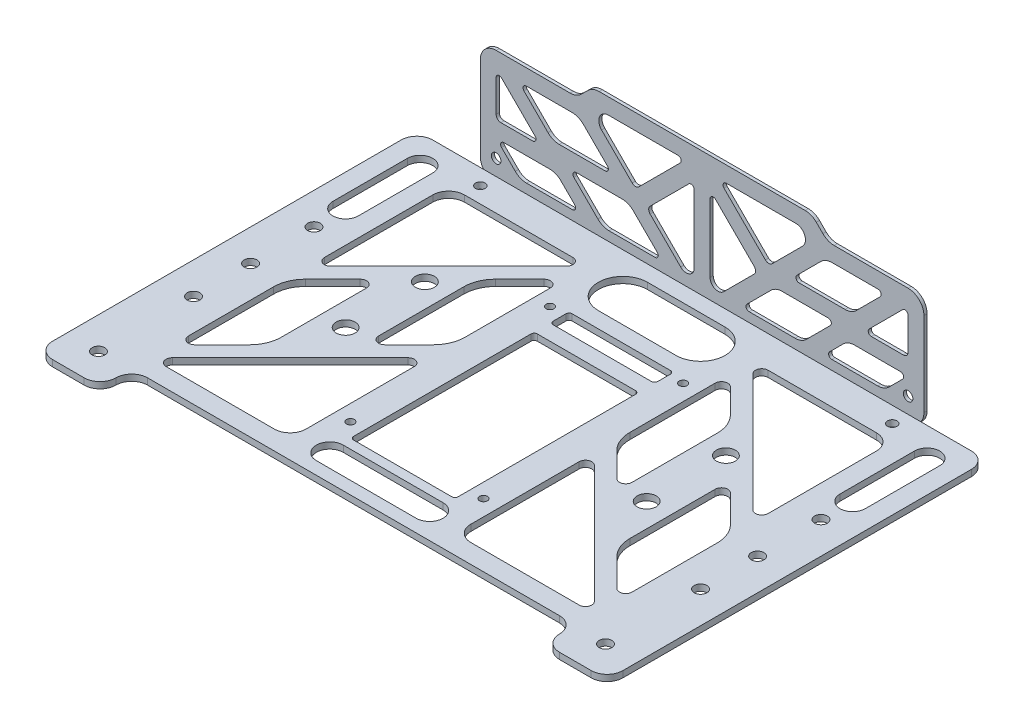
SolidWorks part; units mm, degrees
material "Thornel Mat VMA"
ref_plane "前视基准面" through (0, 0, 0) normal (0, 0, 1) x (1, 0, 0)
ref_plane "上视基准面" through (0, 0, 0) normal (0, 1, 0) x (1, 0, 0)
ref_plane "右视基准面" through (0, 0, 0) normal (1, 0, 0) x (0, 0, -1)
sketch "草图1" plane through (0, 0, 0) normal (0, 1, 0) x (1, 0, 0)
  line L19 (-21, 31.5) -> (21, 31.5) construction
  line L20 (-21, 31.5) -> (-21, -31.5) construction
  line L21 (-21, -31.5) -> (21, -31.5) construction
  line L22 (21, 31.5) -> (21, -31.5) construction
  line L24 (-85, 58.5) -> (85, 58.5)
  line L25 (-90, 53.5) -> (-90, -56.5)
  line L26 (-85, -61.5) -> (-75, -61.5)
  line L28 (0, 0) -> (0, 58.5) construction
  line L29 (-21, 0) -> (0, 0) construction
  line L31 (-65, -51.5) -> (65, -51.5)
  line L33 (-80, -61.5) -> (-80, 58.5) construction
  line L34 (0, -55) -> (0, 55) construction
  line L36 (85, -61.5) -> (75, -61.5)
  line L37 (90, 53.5) -> (90, -56.5)
  line L38 (-70, -56.5) -> (-70, -32.8054) construction
  line L40 (-47.5, 18.5) -> (47.5, 18.5) construction
  line L41 (-47.5, 18.5) -> (-47.5, -6.5) construction
  line L42 (-47.5, -6.5) -> (47.5, -6.5) construction
  line L43 (47.5, 18.5) -> (47.5, -6.5) construction
  circle A6 centre (-21, 31.5) radius 1.25
  circle A7 centre (-21, -31.5) radius 1.25
  circle A8 centre (21, -31.5) radius 1.25
  circle A9 centre (21, 31.5) radius 1.25
  circle A10 centre (-80, -52) radius 2
  circle A11 centre (80, -52) radius 2
  arc A12 (-75, -61.5) -> (-70, -56.5) centre (-75, -56.5) ccw
  arc A13 (-90, -56.5) -> (-85, -61.5) centre (-85, -56.5) ccw
  circle A17 centre (-80, 16) radius 2
  circle A18 centre (-80, -4) radius 2
  circle A19 centre (-80, -22) radius 2
  arc A20 (-85, 58.5) -> (-90, 53.5) centre (-85, 53.5) ccw
  arc A21 (-70, -56.5) -> (-65, -51.5) centre (-65, -56.5) cw
  arc A22 (70, -56.5) -> (65, -51.5) centre (65, -56.5) ccw
  arc A23 (75, -61.5) -> (70, -56.5) centre (75, -56.5) cw
  arc A24 (90, -56.5) -> (85, -61.5) centre (85, -56.5) cw
  circle A25 centre (80, -22) radius 2
  circle A26 centre (80, -4) radius 2
  circle A27 centre (80, 16) radius 2
  arc A28 (85, 58.5) -> (90, 53.5) centre (85, 53.5) cw
  circle A29 centre (-65, 53.5) radius 1.5
  circle A30 centre (65, 53.5) radius 1.5
  circle A33 centre (-47.5, -6.5) radius 3
  circle A34 centre (-47.5, 18.5) radius 3
  circle A35 centre (47.5, 18.5) radius 3
  circle A36 centre (47.5, -6.5) radius 3
  point P21 (0, 31.5)
  dimension "D4" = 120
  dimension "D5" = 20
  dimension "D6" = 4
  dimension "D11" = 180
  dimension "D12" = 30
  dimension "D10" = 20
  dimension "D20" = 2.5
  dimension "D7" = 9.5
  dimension "D8" = 5
  dimension "D3" = 5
  dimension "D13" = 18
  dimension "D14" = 20
  dimension "D15" = 3
  dimension "D16" = 5
  dimension "D17" = 25
  dimension "D24" = 6
  dimension "D9" = 10
  dimension "D18" = 42
  dimension "D19" = 63
  dimension "D21" = 25
  dimension "D22" = 95
  dimension "D23" = 55
extrude "凸台-拉伸1" add sketch "草图1" along normal blind 2
sketch "草图3" plane through (0, 2, 0) normal (0, 1, 0) x (1, 0, 0)
  line L0 (-16.5, 27) -> (-16.5, 33)
  line L5 (16.5, 27) -> (-16.5, 27)
  line L9 (-16.5, 33) -> (16.5, 33)
  line L10 (16.5, 33) -> (16.5, 27)
  line L12 (-16.5, 22) -> (16.5, 22)
  line L13 (-16.5, 22) -> (-16.5, -36)
  line L14 (-16.5, -36) -> (16.5, -36)
  line L15 (16.5, -36) -> (16.5, 22)
  line L41 (0, 27) -> (0, 0) construction
  circle A0 centre (21, 31.5) radius 1.25 construction
  dimension "D4" = 1.5
  dimension "D1" = 5
  dimension "D2" = 33
  dimension "D3" = 58
  dimension "D6" = 6
extrude "切除-拉伸2" cut sketch "草图3" against normal through all
sketch "草图4" plane through (0, 0, -58.5) normal (0, 0, -1) x (-1, 0, 0)
  line L6 (-85, 0) -> (85, 0) construction
  line L13 (-70, 31.5) -> (-70, 5)
  line L14 (-65, 0) -> (65, 0)
  line L15 (-41.6421, 36.5) -> (-65, 36.5)
  line L16 (-90, 2) -> (-90, 0) construction
  line L17 (-85, 2) -> (85, 2) construction
  line L18 (0, 55) -> (0, -55) construction
  line L19 (70, 31.5) -> (70, 5)
  line L20 (-38.1066, 37.9645) -> (-36.0355, 40.0355)
  line L21 (-32.5, 41.5) -> (32.5, 41.5)
  line L22 (38.1066, 37.9645) -> (36.0355, 40.0355)
  line L23 (41.6421, 36.5) -> (65, 36.5)
  circle A0 centre (-65, 7) radius 1.5
  circle A1 centre (65, 7) radius 1.5
  arc A2 (-65, 0) -> (-70, 5) centre (-65, 5) cw
  arc A3 (65, 0) -> (70, 5) centre (65, 5) ccw
  arc A4 (-65, 36.5) -> (-70, 31.5) centre (-65, 31.5) ccw
  arc A5 (-36.0355, 40.0355) -> (-32.5, 41.5) centre (-32.5, 36.5) cw
  arc A6 (-38.1066, 37.9645) -> (-41.6421, 36.5) centre (-41.6421, 41.5) cw
  arc A7 (38.1066, 37.9645) -> (41.6421, 36.5) centre (41.6421, 41.5) ccw
  arc A8 (36.0355, 40.0355) -> (32.5, 41.5) centre (32.5, 36.5) ccw
  arc A9 (65, 36.5) -> (70, 31.5) centre (65, 31.5) cw
  dimension "D1" = 20
  dimension "D2" = 3
  dimension "D3" = 5
  dimension "D4" = 5
  dimension "D5" = 5
  dimension "D6" = 36.5
  dimension "D7" = 5
  dimension "D8" = 5
  dimension "D9" = 65
  dimension "D10" = 135
extrude "凸台-拉伸2" add sketch "草图4" along normal blind 1 separate body
sketch "草图5" plane through (0, 0, -59.5) normal (0, 0, -1) x (-1, 0, 0)
  line L0 (-29.6152, 36.5) -> (-7.5962, 36.5)
  line L1 (-2.5, 29.6967) -> (-2.5, 8.1777)
  line L2 (-6.7678, 6.4099) -> (-16.4237, 16.0659)
  line L3 (32.5, 41.5) -> (-32.5, 41.5) construction
  line L4 (0, 22.825) -> (0, -22.825) construction
  line L5 (52.7071, 19.2071) -> (63.2929, 29.7929)
  line L6 (63.5, 17.5) -> (53.4142, 17.5)
  line L7 (65, 29.0858) -> (65, 19)
  line L8 (45.1079, 20.75) -> (30.5931, 20.75)
  line L9 (-62.5858, 12.5) -> (-48.0711, 12.5)
  line L10 (-63.2929, 10.7929) -> (-58.9645, 6.4645)
  line L11 (-44.5355, 11.0355) -> (-40.2071, 6.7071)
  line L12 (-55.4289, 5) -> (-40.9142, 5)
  line L13 (-55.5147, 31.5) -> (-41, 31.5)
  line L14 (-56.2218, 29.7929) -> (-48.6434, 22.2145)
  line L15 (-37.4645, 30.0355) -> (-29.886, 22.4571)
  line L16 (-45.1079, 20.75) -> (-30.5931, 20.75)
  line L17 (-65, 0) -> (65, 0) construction
  line L23 (-65, 29.0858) -> (-65, 19)
  line L32 (-63.5, 17.5) -> (-53.4142, 17.5)
  line L33 (-52.7071, 19.2071) -> (-63.2929, 29.7929)
  line L34 (-41.6421, 36.5) -> (-65, 36.5) construction
  line L35 (-70, 31.5) -> (-70, 5) construction
  line L36 (37.4645, 30.0355) -> (29.886, 22.4571)
  line L37 (56.2218, 29.7929) -> (48.6434, 22.2145)
  line L38 (55.5147, 31.5) -> (41, 31.5)
  line L39 (55.4289, 5) -> (40.9142, 5)
  line L40 (44.5355, 11.0355) -> (40.2071, 6.7071)
  line L41 (63.2929, 10.7929) -> (58.9645, 6.4645)
  line L42 (62.5858, 12.5) -> (48.0711, 12.5)
  line L43 (6.7678, 6.4099) -> (16.4237, 16.0659)
  line L44 (2.5, 29.6967) -> (2.5, 8.1777)
  line L45 (29.6152, 36.5) -> (7.5962, 36.5)
  line L46 (-6.8891, 34.7929) -> (-19.9593, 21.7227)
  line L47 (-4.2071, 30.4038) -> (-16.4237, 18.1872)
  line L48 (-22.0806, 21.7227) -> (-31.7365, 31.3787)
  line L49 (-29.3579, 5) -> (-14.8431, 5)
  line L50 (-40.4718, 14.0429) -> (-32.8934, 6.4645)
  line L51 (-39.7647, 15.75) -> (-25.25, 15.75)
  line L52 (-21.7145, 14.2855) -> (-14.136, 6.7071)
  line L53 (21.7145, 14.2855) -> (14.136, 6.7071)
  line L54 (39.7647, 15.75) -> (25.25, 15.75)
  line L55 (40.4718, 14.0429) -> (32.8934, 6.4645)
  line L56 (29.3579, 5) -> (14.8431, 5)
  line L57 (4.2071, 30.4038) -> (16.4237, 18.1872)
  line L58 (6.8891, 34.7929) -> (19.9593, 21.7227)
  line L59 (22.0806, 21.7227) -> (31.7365, 31.3787)
  arc A1 (-29.6152, 36.5) -> (-31.7365, 31.3787) centre (-29.6152, 33.5) ccw
  arc A2 (-6.7678, 6.4099) -> (-2.5, 8.1777) centre (-5, 8.1777) ccw
  arc A3 (-56.2218, 29.7929) -> (-55.5147, 31.5) centre (-55.5147, 30.5) cw
  arc A4 (-29.886, 22.4571) -> (-30.5931, 20.75) centre (-30.5931, 21.75) cw
  arc A5 (-63.2929, 10.7929) -> (-62.5858, 12.5) centre (-62.5858, 11.5) cw
  arc A6 (-65, 29.0858) -> (-63.2929, 29.7929) centre (-64, 29.0858) cw
  arc A7 (-40.2071, 6.7071) -> (-40.9142, 5) centre (-40.9142, 6) cw
  arc A8 (-53.4142, 17.5) -> (-52.7071, 19.2071) centre (-53.4142, 18.5) ccw
  arc A9 (-58.9645, 6.4645) -> (-55.4289, 5) centre (-55.4289, 10) ccw
  arc A10 (-48.0711, 12.5) -> (-44.5355, 11.0355) centre (-48.0711, 7.5) cw
  arc A11 (-48.6434, 22.2145) -> (-45.1079, 20.75) centre (-45.1079, 25.75) ccw
  arc A12 (-41, 31.5) -> (-37.4645, 30.0355) centre (-41, 26.5) cw
  arc A14 (-65, 19) -> (-63.5, 17.5) centre (-63.5, 19) ccw
  arc A15 (65, 19) -> (63.5, 17.5) centre (63.5, 19) cw
  arc A17 (41, 31.5) -> (37.4645, 30.0355) centre (41, 26.5) ccw
  arc A18 (48.6434, 22.2145) -> (45.1079, 20.75) centre (45.1079, 25.75) cw
  arc A19 (48.0711, 12.5) -> (44.5355, 11.0355) centre (48.0711, 7.5) ccw
  arc A20 (58.9645, 6.4645) -> (55.4289, 5) centre (55.4289, 10) cw
  arc A21 (53.4142, 17.5) -> (52.7071, 19.2071) centre (53.4142, 18.5) cw
  arc A22 (40.2071, 6.7071) -> (40.9142, 5) centre (40.9142, 6) ccw
  arc A23 (65, 29.0858) -> (63.2929, 29.7929) centre (64, 29.0858) ccw
  arc A24 (63.2929, 10.7929) -> (62.5858, 12.5) centre (62.5858, 11.5) ccw
  arc A25 (29.886, 22.4571) -> (30.5931, 20.75) centre (30.5931, 21.75) ccw
  arc A26 (56.2218, 29.7929) -> (55.5147, 31.5) centre (55.5147, 30.5) ccw
  arc A27 (6.7678, 6.4099) -> (2.5, 8.1777) centre (5, 8.1777) cw
  arc A28 (29.6152, 36.5) -> (31.7365, 31.3787) centre (29.6152, 33.5) cw
  arc A29 (-16.4237, 18.1872) -> (-16.4237, 16.0659) centre (-15.3631, 17.1265) ccw
  arc A30 (-22.0806, 21.7227) -> (-19.9593, 21.7227) centre (-21.0199, 22.7834) ccw
  arc A31 (-7.5962, 36.5) -> (-6.8891, 34.7929) centre (-7.5962, 35.5) cw
  arc A32 (-2.5, 29.6967) -> (-4.2071, 30.4038) centre (-3.5, 29.6967) ccw
  arc A33 (-40.4718, 14.0429) -> (-39.7647, 15.75) centre (-39.7647, 14.75) cw
  arc A34 (-25.25, 15.75) -> (-21.7145, 14.2855) centre (-25.25, 10.75) cw
  arc A35 (-14.136, 6.7071) -> (-14.8431, 5) centre (-14.8431, 6) cw
  arc A36 (-32.8934, 6.4645) -> (-29.3579, 5) centre (-29.3579, 10) ccw
  arc A37 (25.25, 15.75) -> (21.7145, 14.2855) centre (25.25, 10.75) ccw
  arc A38 (40.4718, 14.0429) -> (39.7647, 15.75) centre (39.7647, 14.75) ccw
  arc A39 (32.8934, 6.4645) -> (29.3579, 5) centre (29.3579, 10) cw
  arc A40 (16.4237, 18.1872) -> (16.4237, 16.0659) centre (15.3631, 17.1265) cw
  arc A41 (2.5, 29.6967) -> (4.2071, 30.4038) centre (3.5, 29.6967) cw
  arc A42 (22.0806, 21.7227) -> (19.9593, 21.7227) centre (21.0199, 22.7834) cw
  arc A43 (7.5962, 36.5) -> (6.8891, 34.7929) centre (7.5962, 35.5) ccw
  arc A44 (14.136, 6.7071) -> (14.8431, 5) centre (14.8431, 6) ccw
  point P33 (-65, 12.5)
  point P36 (-65, 31.5)
  point P43 (-57.5, 5)
  point P98 (57.5, 5)
  dimension "D8" = 5
  dimension "D10" = 3
  dimension "D11" = 1
  dimension "D12" = 5
  dimension "D13" = 5
  dimension "D15" = 2.5
  dimension "D16" = 1.5
  dimension "D17" = 2
  dimension "D1" = 5
  dimension "D2" = 5
  dimension "D3" = 5
  dimension "D4" = 5
  dimension "D5" = 5
  dimension "D6" = 7.5
  dimension "D7" = 135
  dimension "D9" = 5
  dimension "D14" = 5
  dimension "D18" = 5
extrude "切除-拉伸3" cut sketch "草图5" against normal through all
sketch "草图6" plane through (0, 2, 0) normal (0, 1, 0) x (1, 0, 0)
  line L0 (-65, 48.5) -> (-30.8284, 48.5)
  line L1 (-29.4142, 45.0858) -> (-66.5858, 7.9142)
  line L2 (-70, 9.3284) -> (-70, 43.5)
  line L3 (-26, -6.3284) -> (-26, -40.5)
  line L4 (-31, -45.5) -> (-65.1716, -45.5)
  line L5 (-66.5858, -42.0858) -> (-29.4142, -4.9142)
  line L6 (-55, 7.6005) -> (-55, -19.2868)
  line L7 (-57.9289, -26.3579) -> (-66.5858, -35.0147)
  line L8 (-70, -33.6005) -> (-70, -6.7132)
  line L9 (-67.0711, 0.3579) -> (-58.4142, 9.0147)
  line L10 (-40, 23.2868) -> (-40, -3.6005)
  line L11 (-36.5858, -5.0147) -> (-28.9289, 2.6421)
  line L12 (-26, 9.7132) -> (-26, 36.6005)
  line L13 (-29.4142, 38.0147) -> (-37.0711, 30.3579)
  line L14 (-65, -51.5) -> (65, -51.5) construction
  line L15 (-90, 53.5) -> (-90, -56.5) construction
  line L16 (85, 58.5) -> (-85, 58.5) construction
  line L17 (-12.25, 45.75) -> (12.25, 45.75) construction
  line L18 (-12.25, 53.5) -> (12.25, 53.5)
  line L19 (-12.25, 38) -> (12.25, 38)
  line L20 (15.75, -43.25) -> (-15.75, -43.25) construction
  line L21 (15.75, -47.5) -> (-15.75, -47.5)
  line L22 (15.75, -39) -> (-15.75, -39)
  line L23 (0, 45.75) -> (0, -43.25) construction
  line L24 (16.5, 33) -> (-16.5, 33) construction
  line L25 (-16.5, -36) -> (16.5, -36) construction
  line L27 (0, -22.825) -> (0, 22.825) construction
  line L28 (29.4142, 38.0147) -> (37.0711, 30.3579)
  line L29 (26, 9.7132) -> (26, 36.6005)
  line L30 (36.5858, -5.0147) -> (28.9289, 2.6421)
  line L31 (40, 23.2868) -> (40, -3.6005)
  line L32 (67.0711, 0.3579) -> (58.4142, 9.0147)
  line L33 (70, -33.6005) -> (70, -6.7132)
  line L34 (57.9289, -26.3579) -> (66.5858, -35.0147)
  line L35 (55, 7.6005) -> (55, -19.2868)
  line L36 (66.5858, -42.0858) -> (29.4142, -4.9142)
  line L37 (31, -45.5) -> (65.1716, -45.5)
  line L38 (26, -6.3284) -> (26, -40.5)
  line L39 (70, 9.3284) -> (70, 43.5)
  line L40 (29.4142, 45.0858) -> (66.5858, 7.9142)
  line L41 (65, 48.5) -> (30.8284, 48.5)
  line L42 (-80, 49.5) -> (-80, 26) construction
  line L43 (-76, 49.5) -> (-76, 26)
  line L44 (-84, 49.5) -> (-84, 26)
  line L45 (-80, 16) -> (-80, 26) construction
  line L46 (80, 49.5) -> (80, 26) construction
  line L47 (76, 49.5) -> (76, 26)
  line L48 (84, 49.5) -> (84, 26)
  circle A0 centre (-21, -31.5) radius 1.25 construction
  circle A1 centre (-47.5, -6.5) radius 3 construction
  arc A2 (-12.25, 53.5) -> (-12.25, 38) centre (-12.25, 45.75) ccw
  arc A3 (12.25, 38) -> (12.25, 53.5) centre (12.25, 45.75) ccw
  arc A4 (15.75, -47.5) -> (15.75, -39) centre (15.75, -43.25) ccw
  arc A5 (-15.75, -39) -> (-15.75, -47.5) centre (-15.75, -43.25) ccw
  arc A6 (-28.9289, 2.6421) -> (-26, 9.7132) centre (-36, 9.7132) ccw
  arc A7 (-40, 23.2868) -> (-37.0711, 30.3579) centre (-30, 23.2868) cw
  arc A8 (-55, -19.2868) -> (-57.9289, -26.3579) centre (-65, -19.2868) cw
  arc A9 (-70, -6.7132) -> (-67.0711, 0.3579) centre (-60, -6.7132) cw
  arc A10 (-26, -40.5) -> (-31, -45.5) centre (-31, -40.5) cw
  arc A11 (-65, 48.5) -> (-70, 43.5) centre (-65, 43.5) ccw
  arc A12 (-66.5858, 7.9142) -> (-70, 9.3284) centre (-68, 9.3284) cw
  arc A13 (-30.8284, 48.5) -> (-29.4142, 45.0858) centre (-30.8284, 46.5) cw
  arc A14 (-26, 36.6005) -> (-29.4142, 38.0147) centre (-28, 36.6005) ccw
  arc A15 (-40, -3.6005) -> (-36.5858, -5.0147) centre (-38, -3.6005) ccw
  arc A16 (-55, 7.6005) -> (-58.4142, 9.0147) centre (-57, 7.6005) ccw
  arc A17 (-66.5858, -35.0147) -> (-70, -33.6005) centre (-68, -33.6005) cw
  arc A18 (-65.1716, -45.5) -> (-66.5858, -42.0858) centre (-65.1716, -43.5) cw
  arc A19 (-26, -6.3284) -> (-29.4142, -4.9142) centre (-28, -6.3284) ccw
  arc A20 (26, -6.3284) -> (29.4142, -4.9142) centre (28, -6.3284) cw
  arc A21 (65.1716, -45.5) -> (66.5858, -42.0858) centre (65.1716, -43.5) ccw
  arc A22 (66.5858, -35.0147) -> (70, -33.6005) centre (68, -33.6005) ccw
  arc A23 (55, 7.6005) -> (58.4142, 9.0147) centre (57, 7.6005) cw
  arc A24 (40, -3.6005) -> (36.5858, -5.0147) centre (38, -3.6005) cw
  arc A25 (26, 36.6005) -> (29.4142, 38.0147) centre (28, 36.6005) cw
  arc A26 (30.8284, 48.5) -> (29.4142, 45.0858) centre (30.8284, 46.5) ccw
  arc A27 (66.5858, 7.9142) -> (70, 9.3284) centre (68, 9.3284) ccw
  arc A28 (65, 48.5) -> (70, 43.5) centre (65, 43.5) cw
  arc A29 (26, -40.5) -> (31, -45.5) centre (31, -40.5) ccw
  arc A30 (70, -6.7132) -> (67.0711, 0.3579) centre (60, -6.7132) ccw
  arc A31 (55, -19.2868) -> (57.9289, -26.3579) centre (65, -19.2868) ccw
  arc A32 (40, 23.2868) -> (37.0711, 30.3579) centre (30, 23.2868) ccw
  arc A33 (28.9289, 2.6421) -> (26, 9.7132) centre (36, 9.7132) cw
  arc A34 (-76, 49.5) -> (-84, 49.5) centre (-80, 49.5) ccw
  arc A35 (-84, 26) -> (-76, 26) centre (-80, 26) ccw
  arc A36 (76, 49.5) -> (84, 49.5) centre (80, 49.5) cw
  arc A37 (84, 26) -> (76, 26) centre (80, 26) cw
  point P20 (0, 45.75)
  point P31 (0, -43.25)
  point P43 (-20, 45.75)
  point P44 (-20, -43.25)
  point P45 (-80, 37.75)
  point P65 (-26, 48.5)
  point P76 (-70, -45.5)
  point P123 (70, -45.5)
  point P124 (26, 48.5)
  point P135 (80, 37.75)
  dimension "D5" = 5
  dimension "D6" = 7.5
  dimension "D7" = 7.5
  dimension "D14" = 6
  dimension "D17" = 10
  dimension "D18" = 5
  dimension "D19" = 2
  dimension "D21" = 10
  dimension "D1" = 6
  dimension "D2" = 20
  dimension "D3" = 10
  dimension "D4" = 45
  dimension "D8" = 5
  dimension "D9" = 5
  dimension "D10" = 45
  dimension "D11" = 5
  dimension "D12" = 5
  dimension "D13" = 6
  dimension "D15" = 4
  dimension "D16" = 3
  dimension "D20" = 8
extrude "切除-拉伸4" cut sketch "草图6" against normal through all
fillet "圆角1" radius 1 8 edges at (16.5, 1, 36) (-16.5, 1, 36) (16.5, 1, -22) (-16.5, 1, -22) (16.5, 1, -27) (-16.5, 1, -27) (16.5, 1, -33) (-16.5, 1, -33)
